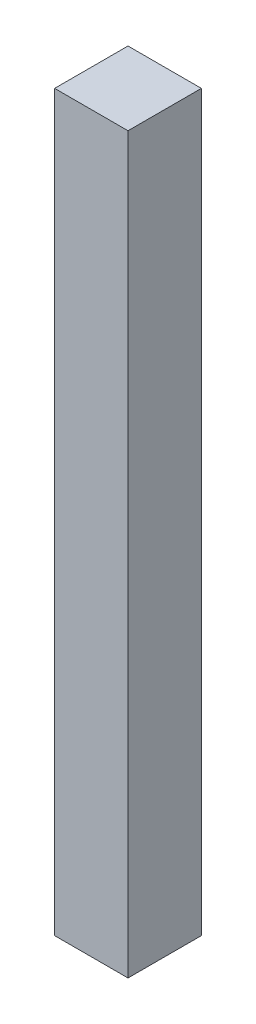
SolidWorks part; units mm, degrees
material "1060 Alloy"
ref_plane "Front Plane" through (0, 0, 0) normal (0, 0, 1) x (1, 0, 0)
ref_plane "Top Plane" through (0, 0, 0) normal (0, 1, 0) x (1, 0, 0)
ref_plane "Right Plane" through (0, 0, 0) normal (1, 0, 0) x (0, 0, -1)
sketch "Sketch1" plane through (0, 0, 0) normal (0, 1, 0) x (1, 0, 0)
  line L1 (-3.175, -3.175) -> (3.175, -3.175)
  line L2 (-3.175, -3.175) -> (-3.175, 3.175)
  line L3 (-3.175, 3.175) -> (3.175, 3.175)
  line L4 (3.175, -3.175) -> (3.175, 3.175)
  line L5 (-3.175, -3.175) -> (3.175, 3.175) construction
  line L6 (-3.175, 3.175) -> (3.175, -3.175) construction
  point P0 (0, 0)
  dimension "D1" = 6.35
extrude "Boss-Extrude1" add sketch "Sketch1" along normal blind 63.5
